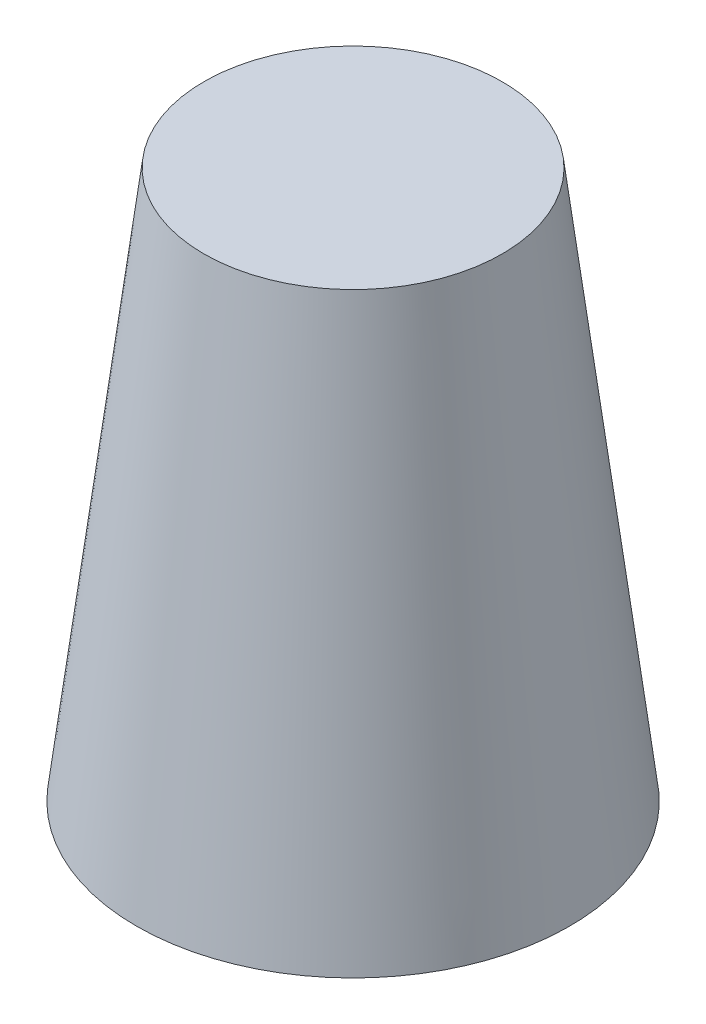
SolidWorks part; units mm, degrees
ref_plane "Front Plane" through (0, 0, 0) normal (0, 0, 1) x (1, 0, 0)
ref_plane "Top Plane" through (0, 0, 0) normal (0, 1, 0) x (1, 0, 0)
ref_plane "Right Plane" through (0, 0, 0) normal (1, 0, 0) x (0, 0, -1)
sketch "Sketch1" plane through (0, 0, 0) normal (0, 1, 0) x (1, 0, 0)
  circle A0 centre (0, 0) radius 47.625
extrude "Boss-Extrude1" add sketch "Sketch1" along normal blind 120.65 draft 7
